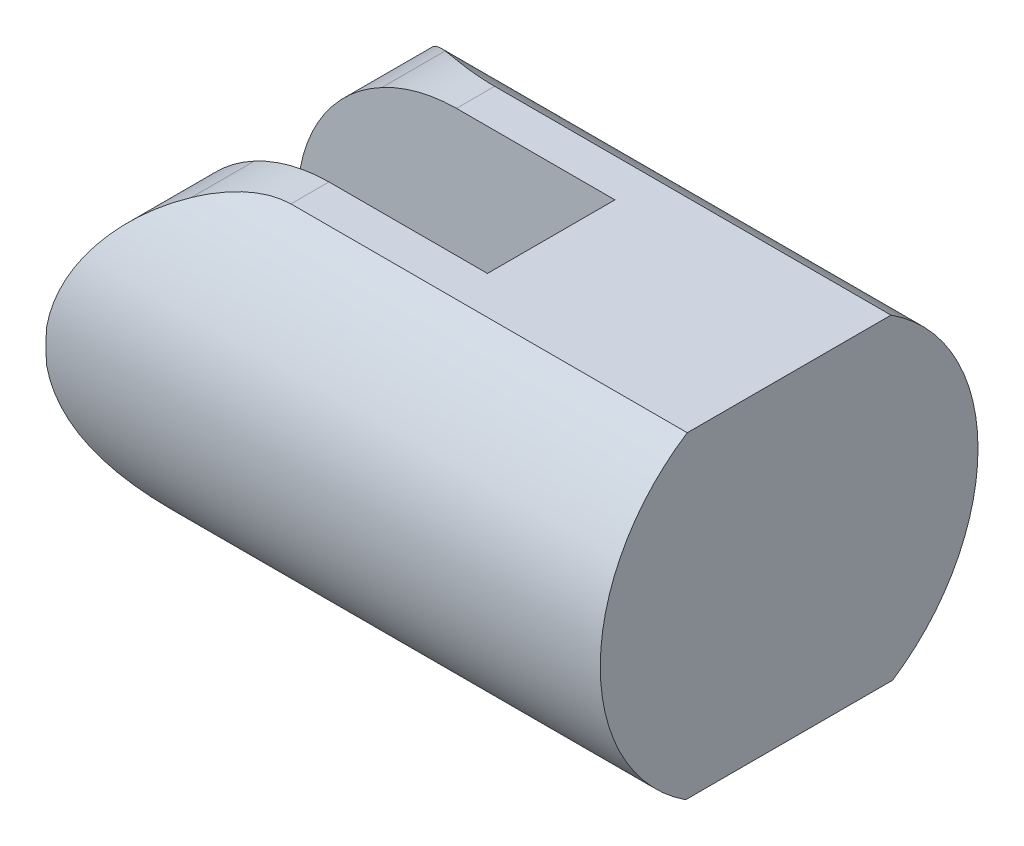
SolidWorks part; units mm, degrees
material "ABS"
ref_plane "Płaszczyzna XY" through (0, 0, 0) normal (0, 0, 1) x (1, 0, 0)
ref_plane "Płaszczyzna XZ" through (0, 0, 0) normal (0, 1, 0) x (1, 0, 0)
ref_plane "Płaszczyzna YZ" through (0, 0, 0) normal (1, 0, 0) x (0, 0, -1)
sketch "Sketch1" plane through (0, 0, 0) normal (0, 0, 1) x (1, 0, 0)
  line L0 (-6.75, 0.6975) -> (-6.75, -0.7208)
  line L1 (-3.2195, -5.9313) -> (16.8249, -5.9313)
  line L2 (16.8249, -5.9313) -> (16.8249, 5.9313)
  line L3 (16.8249, 5.9313) -> (-3.1751, 5.9313)
  arc A0 (-6.75, -0.7208) -> (-3.2195, -5.9313) centre (-0.0931, -0.0116) ccw
  arc A1 (-3.1751, 5.9313) -> (-6.75, 0.6975) centre (-0.0931, -0.0116) ccw
  dimension "D2" = 6.6946
  dimension "D1" = 6.6569
  dimension "D3" = 20
  dimension "D4" = 0.0931
  dimension "D5" = 3.1751
  dimension "D6" = 3.2195
  dimension "D7" = 0.6975
extrude "Boss-Extrude1" add sketch "Sketch1" along normal blind 13.5
sketch "Sketch2" plane through (-6.75, 0, 0) normal (-1, 0, 0) x (0, 0, 1)
  line L0 (4.05, 7) -> (4.05, -7)
  line L1 (4.05, 7) -> (9.45, 7)
  line L2 (4.05, -7) -> (9.45, -7)
  line L3 (9.45, 7) -> (9.45, -7)
  line L4 (4.05, 7) -> (9.45, -7) construction
  line L5 (4.05, -7) -> (9.45, 7) construction
  line L8 (13.5, 0.6975) -> (13.5, -0.7208) construction
  point P1 (6.75, 0)
  dimension "D1" = 14
  dimension "D2" = 5.4
  dimension "D3" = 6.75
extrude "Cut-Extrude1" cut sketch "Sketch2" against normal blind 13.5
sketch "Sketch3" plane through (16.8249, 0, 0) normal (1, 0, 0) x (0, 0, -1)
  line L0 (-13.5, -5.9313) -> (-13.5, 5.9313) construction
  line L2 (-13.5, -5.9313) -> (0, -5.9313) construction
  circle A0 centre (-6.7466, 0) radius 8
  circle A1 centre (-6.7466, 0) radius 12.1528
  dimension "D1" = 16
  dimension "D2" = 6.7534
  dimension "D3" = 5.9313
extrude "Cut-Extrude2" cut sketch "Sketch3" against normal through all
sketch "Sketch4" plane through (16.8249, 0, 0) normal (1, 0, 0) x (0, 0, -1)
  line L4 (-13.5, 4.2885) -> (-13.5, -4.2885)
  line L5 (-12.1149, -5.9313) -> (-1.3782, -5.9313)
  line L6 (0, -4.2993) -> (0, 4.2993)
  line L7 (-1.3782, 5.9313) -> (-12.1149, 5.9313)
  line L8 (-13.5, 4.2885) -> (-13.5, -4.2885)
  line L9 (-12.1149, -5.9313) -> (-1.3782, -5.9313)
  line L10 (0, -4.2993) -> (0, 4.2993)
  line L11 (-1.3782, 5.9313) -> (-12.1149, 5.9313)
  circle A0 centre (-6.7466, 0) radius 8
  arc A4 (-12.1149, 5.9313) -> (-13.5, 4.2885) centre (-6.7466, 0) ccw
  arc A5 (-13.5, -4.2885) -> (-12.1149, -5.9313) centre (-6.7466, 0) ccw
  arc A6 (-1.3782, -5.9313) -> (0, -4.2993) centre (-6.7466, 0) ccw
  arc A7 (0, 4.2993) -> (-1.3782, 5.9313) centre (-6.7466, 0) ccw
  arc A8 (-12.1149, 5.9313) -> (-13.5, 4.2885) centre (-6.7466, 0) ccw
  arc A9 (-13.5, -4.2885) -> (-12.1149, -5.9313) centre (-6.7466, 0) ccw
  arc A10 (-1.3782, -5.9313) -> (0, -4.2993) centre (-6.7466, 0) ccw
  arc A11 (0, 4.2993) -> (-1.3782, 5.9313) centre (-6.7466, 0) ccw
  line M10 (-13.5, 4.2885) -> (-13.5, -4.2885)
  line M12 (-12.1149, -5.9313) -> (-1.3782, -5.9313)
  line M14 (0, -4.2993) -> (0, 4.2993)
  line M16 (-1.3782, 5.9313) -> (-12.1149, 5.9313)
  dimension "D1" = 0
extrude "Boss-Extrude2" add sketch "Sketch4" against normal blind 32.5 contours A0 M12 | A0 M10 | A0 M16 | A0 M14
ref_plane "Plane1" through (0, 0, -10) normal (0, 0, 1) x (1, 0, 0)
sketch "Sketch7" plane through (0, 0, -10) normal (0, 0, 1) x (1, 0, 0)
  line L0 (-6.6569, -0.7091) -> (-6.6569, 0.7091)
  line L1 (0.0372, 6.7369) -> (17.6313, 6.7369)
  line L2 (17.6313, 6.7369) -> (17.6313, 9.9367)
  line L3 (17.6313, 9.9367) -> (-17.1529, 9.9367)
  line L4 (-17.1529, 9.9367) -> (-17.7693, -9.1332)
  line L5 (-17.7693, -9.1332) -> (18.7538, -9.1332)
  line L6 (18.7538, -9.1332) -> (18.7538, -6.693)
  line L7 (18.7538, -6.693) -> (0.1483, -6.693)
  arc A0 (-3.1264, 5.9197) -> (-5.1414, 4.2877) centre (0, 0) ccw
  arc A1 (-5.1414, 4.2877) -> (-6.6569, 0.7091) centre (0, 0) ccw
  arc A2 (-6.6569, -0.7091) -> (-5.1219, -4.3109) centre (0, 0) ccw
  arc A3 (-5.1219, -4.3109) -> (-3.082, -5.943) centre (0, 0) ccw
  arc A4 (-3.1264, 5.9197) -> (0.0372, 6.7369) centre (0.0931, -0.0116) cw
  arc A5 (-3.082, -5.943) -> (0.1483, -6.693) centre (0, 0) ccw
  point P16 (0.0931, -0.0116)
extrude "Cut-Extrude4" cut sketch "Sketch7" along normal through all
sketch "Sketch8" plane through (0, -6.693, 0) normal (0, -1, 0) x (1, 0, 0)
  line L0 (6.75, 4.05) -> (6.75, 9.45) construction
  line L1 (6.75, 4.05) -> (6.75, 9.45)
  line L2 (6.75, 4.05) -> (-8.9654, 4.05)
  line L3 (-8.9654, 4.05) -> (-8.9654, 9.45)
  line L4 (-8.9654, 9.45) -> (6.75, 9.45)
extrude "Cut-Extrude5" cut sketch "Sketch8" against normal blind 23.5
